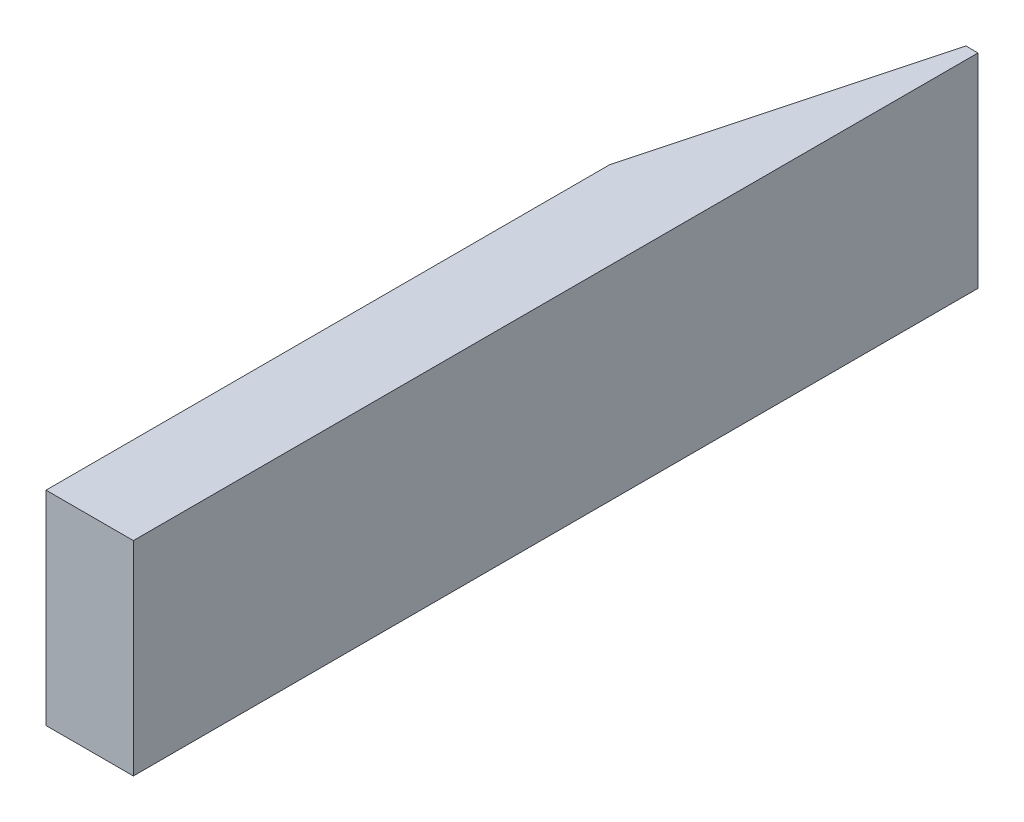
SolidWorks part; units mm, degrees
ref_plane "Front Plane" through (0, 0, 0) normal (0, 0, 1) x (1, 0, 0)
ref_plane "Top Plane" through (0, 0, 0) normal (0, 1, 0) x (1, 0, 0)
ref_plane "Right Plane" through (0, 0, 0) normal (1, 0, 0) x (0, 0, -1)
sketch "Sketch1" plane through (0, 0, 0) normal (0, 0, 1) x (1, 0, 0)
  line L1 (0, 0) -> (38.1, 0)
  line L2 (0, 0) -> (0, 88.9)
  line L3 (0, 88.9) -> (38.1, 88.9)
  line L4 (38.1, 0) -> (38.1, 88.9)
  dimension "D1" = 38.1
  dimension "D2" = 88.9
extrude "Boss-Extrude1" add sketch "Sketch1" along normal blind 368.3
chamfer "Chamfer1" distance 32.86 angle 75 1 edges at (0, 44.45, 0)
